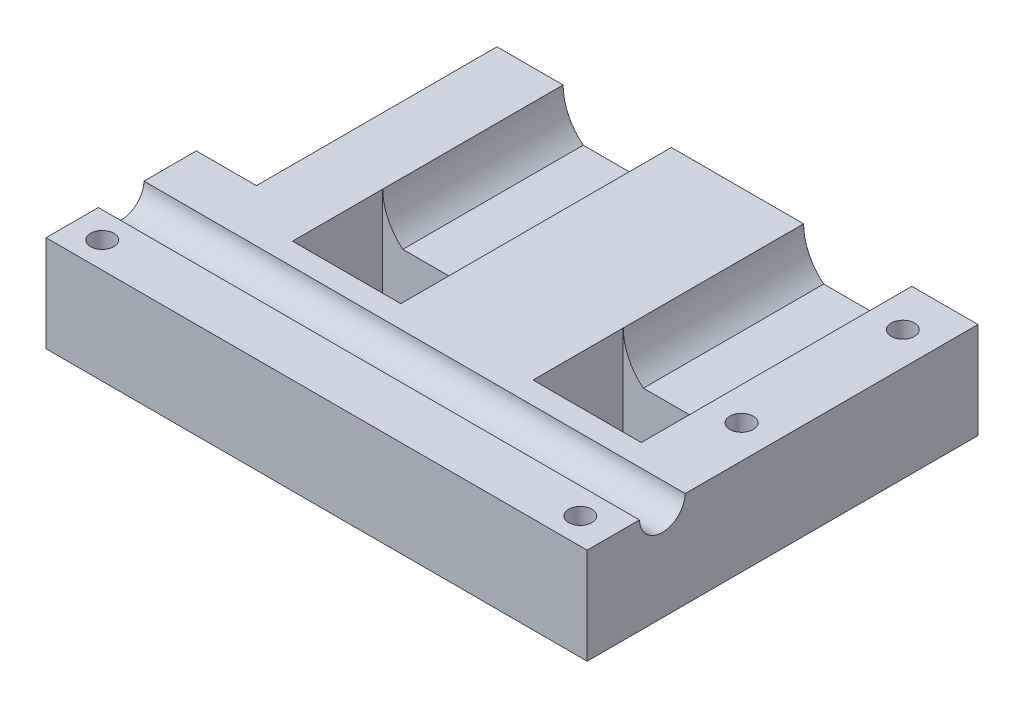
SolidWorks part; units mm, degrees
ref_plane "Front Plane" through (0, 0, 0) normal (0, 0, 1) x (1, 0, 0)
ref_plane "Top Plane" through (0, 0, 0) normal (0, 1, 0) x (1, 0, 0)
ref_plane "Right Plane" through (0, 0, 0) normal (1, 0, 0) x (0, 0, -1)
sketch "Sketch1" plane through (0, 0, 0) normal (0, 0, 1) x (1, 0, 0)
  line L0 (-50.8, 0) -> (50.8, 0)
  line L1 (50.8, 0) -> (50.8, 20.32)
  line L2 (50.8, 20.32) -> (36.83, 20.32)
  line L3 (25.4, 20.32) -> (51.7323, 20.32) construction
  line L4 (13.97, 20.32) -> (-13.97, 20.32)
  line L5 (32.5842, 11.43) -> (18.2158, 11.43)
  line L6 (0, 0) -> (0, 35.6145) construction
  line L7 (-25.4, 20.32) -> (-51.7323, 20.32) construction
  line L8 (-32.5842, 11.43) -> (-18.2158, 11.43)
  line L9 (-50.8, 20.32) -> (-36.83, 20.32)
  line L10 (-50.8, 0) -> (-50.8, 20.32)
  arc A0 (13.97, 20.32) -> (18.2158, 11.43) centre (25.4, 20.32) ccw
  arc A1 (32.5842, 11.43) -> (36.83, 20.32) centre (25.4, 20.32) ccw
  arc A2 (-32.5842, 11.43) -> (-36.83, 20.32) centre (-25.4, 20.32) cw
  arc A3 (-13.97, 20.32) -> (-18.2158, 11.43) centre (-25.4, 20.32) cw
  point P13 (43.815, 20.32)
  point P20 (0, 20.32)
  point P23 (-43.815, 20.32)
  dimension "D1" = 22.86
  dimension "D2" = 8.89
  dimension "D3" = 20.32
  dimension "D4" = 25.4
  dimension "D5" = 50.8
extrude "Boss-Extrude1" add sketch "Sketch1" along normal blind 38.1
sketch "Sketch7" plane through (0, 0, 38.1) normal (0, 0, 1) x (1, 0, 0)
  line L1 (-50.8, 20.32) -> (50.8, 20.32)
  line L2 (-50.8, 20.32) -> (-50.8, 0)
  line L3 (-50.8, 0) -> (50.8, 0)
  line L4 (50.8, 20.32) -> (50.8, 0)
extrude "Boss-Extrude2" add sketch "Sketch7" along normal blind 44.45
sketch "Sketch20" [suppressed] plane through (50.8, 0, 0) normal (1, 0, 0) x (0, 0, -1)
  line L0 (-82.55, 0) -> (-82.55, 20.32) construction
  line L1 (0, 0) -> (-82.55, 0)
  line L2 (0, 0) -> (0, 7.112)
  line L3 (0, 7.112) -> (-50.8, 7.112)
  line L4 (-82.55, 0) -> (-82.55, 3.8743)
  line L5 (-82.55, 20.32) -> (0, 20.32) construction
  line L6 (-82.55, 0) -> (-50.8, 0)
  line L7 (-82.55, 0) -> (-82.55, 20.32)
  line L8 (-82.55, 20.32) -> (-50.8, 20.32)
  line L9 (-50.8, 7.112) -> (-50.8, 20.32)
  dimension "D1" = 50.8
  dimension "D2" = 7.112
extrude "Boss-Extrude8" [suppressed] add sketch "Sketch20" along normal blind 12.7
sketch "Sketch21" plane through (-50.8, 0, 0) normal (-1, 0, 0) x (0, 0, 1)
  line L0 (82.55, 20.32) -> (82.55, 0) construction
  line L1 (0, 0) -> (82.55, 0)
  line L2 (0, 0) -> (0, 7.112)
  line L3 (0, 7.112) -> (50.8, 7.112)
  line L4 (82.55, 0) -> (82.55, 7.1535)
  line L5 (82.55, 20.32) -> (0, 20.32) construction
  line L6 (82.55, 0) -> (68.4145, 0)
  line L7 (82.55, 0) -> (82.55, 20.32)
  line L8 (82.55, 20.32) -> (50.8, 20.32)
  line L9 (50.8, 7.112) -> (50.8, 20.32)
  line L10 (0, 20.32) -> (0, 0) construction
  point P15 (50.8, 13.716)
  line M9 (0, 20.32) -> (0, 0)
  line M10 (0, 0) -> (82.55, 0)
  line M11 (82.55, 0) -> (82.55, 20.32)
  line M12 (82.55, 20.32) -> (0, 20.32)
  dimension "D1" = 7.112
  dimension "D2" = 50.8
extrude "Boss-Extrude9" add sketch "Sketch21" along normal blind 12.7 contours L9 L3 L1 M9 M10 M11 M12
sketch "Sketch8" plane through (0, 20.32, 0) normal (0, 1, 0) x (1, 0, 0)
  line L0 (0, 0) -> (0, -81.5203) construction
  line L1 (-13.97, -38.1) -> (-13.97, 0) construction
  line L2 (-36.83, -38.1) -> (-13.97, -38.1)
  line L3 (-36.83, -38.1) -> (-36.83, -57.15)
  line L4 (-36.83, -57.15) -> (-13.97, -57.15)
  line L5 (-13.97, -38.1) -> (-13.97, -57.15)
  line L6 (13.97, -38.1) -> (13.97, -57.15)
  line L7 (36.83, -57.15) -> (13.97, -57.15)
  line L8 (36.83, -38.1) -> (36.83, -57.15)
  line L9 (36.83, -38.1) -> (13.97, -38.1)
  line L11 (-63.5, -50.8) -> (-50.8, -50.8) construction
  line L12 (-63.5, -50.8) -> (-50.8, -50.8) construction
  line L13 (50.8, 0) -> (36.83, 0) construction
  line L14 (50.8, 0) -> (36.83, 0) construction
  point P16 (-57.15, -50.8)
  point P19 (43.815, 0)
  dimension "D1" = 19.05
extrude "Cut-Extrude1" cut sketch "Sketch8" against normal up to surface (20.32 mm away) up to face at (-6.35, 0, 41.275)
hole_wizard "#10 (0.1935) Diameter Hole1" positions "Sketch4" profile "Sketch5" hole size "#10" standard "ANSI Inch"
sketch "Sketch4" plane through (0, 20.32, 0) normal (0, 1, 0) x (1, 0, 0)
  point P0 (-57.15, -8.89)
  dimension "D2" = 8.89
sketch "Sketch5" plane through (-57.15, 20.32, 8.89) normal (1, 0, 0) x (0, 0, 1)
  line L0 (0, 0) -> (0, 25.4)
  line L1 (0, 25.4) -> (2.4574, 23.9234)
  line L2 (2.4574, 23.9234) -> (2.4574, 0)
  line L5 (2.4574, 0) -> (0, 0)
  line L10 (0, 25.4) -> (-2.4575, 23.9234) construction
  line L11 (0, -6.35) -> (0, 107.95) construction
  dimension "Hole Dia." = 4.9149
  dimension "Hole Depth" = 25.4
  dimension "Drill Angle" = 118
sketch "Sketch9" plane through (-50.8, 0, 0) normal (-1, 0, 0) x (0, 0, 1)
  line L0 (82.55, 20.32) -> (50.8, 20.32) construction
  line L2 (0, 20.32) -> (0, 7.112) construction
  line L3 (82.55, 20.32) -> (71.4993, 20.32) construction
  line L4 (38.1, 20.32) -> (57.15, 20.32) construction
  line L5 (38.1, 20.32) -> (57.15, 20.32) construction
  circle A0 centre (66.675, 20.447) radius 4.826
  point P11 (47.625, 20.32)
  point P12 (77.0247, 20.32)
  dimension "D2" = 9.652
  dimension "D1" = 66.675
  dimension "D3" = 0.127
extrude "Cut-Extrude2" cut sketch "Sketch9" against normal up to surface and the other way up to surface
pattern_linear "LPattern1" count 3 spacing 34.0673 along (0, 0, 1) count 2 spacing 100.965 along (1, 0, 0) of "#10 (0.1935) Diameter Hole1"
